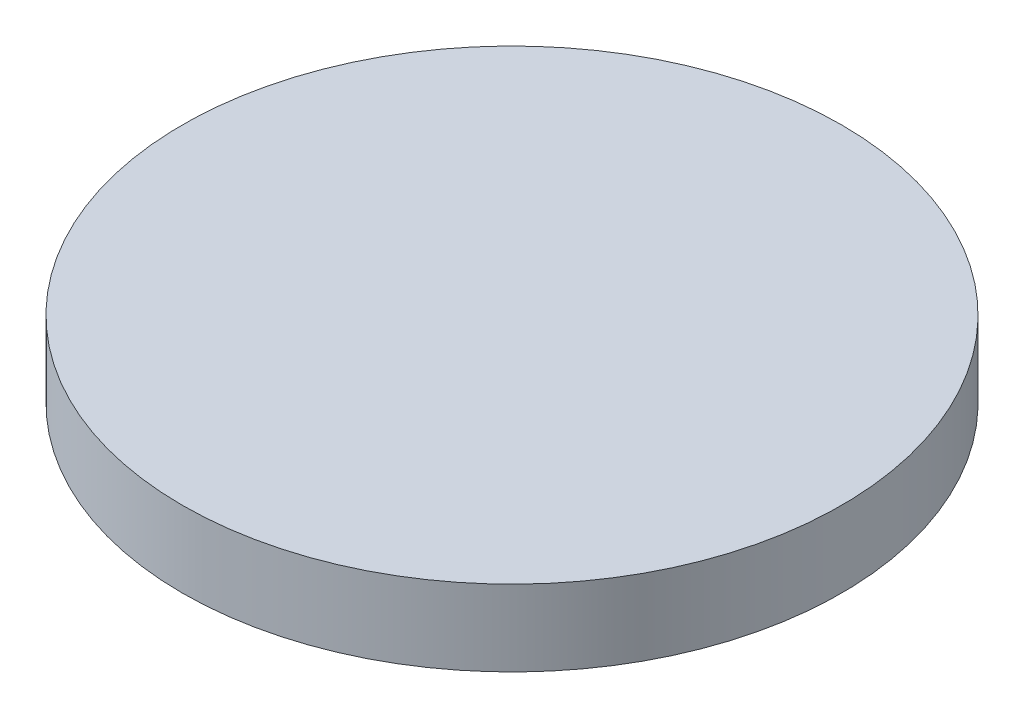
SolidWorks part; units mm, degrees
ref_plane "Front Plane" through (0, 0, 0) normal (0, 0, 1) x (1, 0, 0)
ref_plane "Top Plane" through (0, 0, 0) normal (0, 1, 0) x (1, 0, 0)
ref_plane "Right Plane" through (0, 0, 0) normal (1, 0, 0) x (0, 0, -1)
sketch "Sketch1" plane through (0, 0, 0) normal (0, 1, 0) x (1, 0, 0)
  circle A0 centre (0, 0) radius 39
  circle A1 centre (0, 0) radius 30
  dimension "D1" = 78
  dimension "D2" = 60
extrude "Boss-Extrude7" add sketch "Sketch1" along normal blind 5 contours A1
sketch "Sketch8" plane through (0, 5, 0) normal (0, 1, 0) x (1, 0, 0)
  circle A0 centre (0, 0) radius 39
  dimension "D1" = 78
extrude "Boss-Extrude8" add sketch "Sketch8" along normal blind 9
